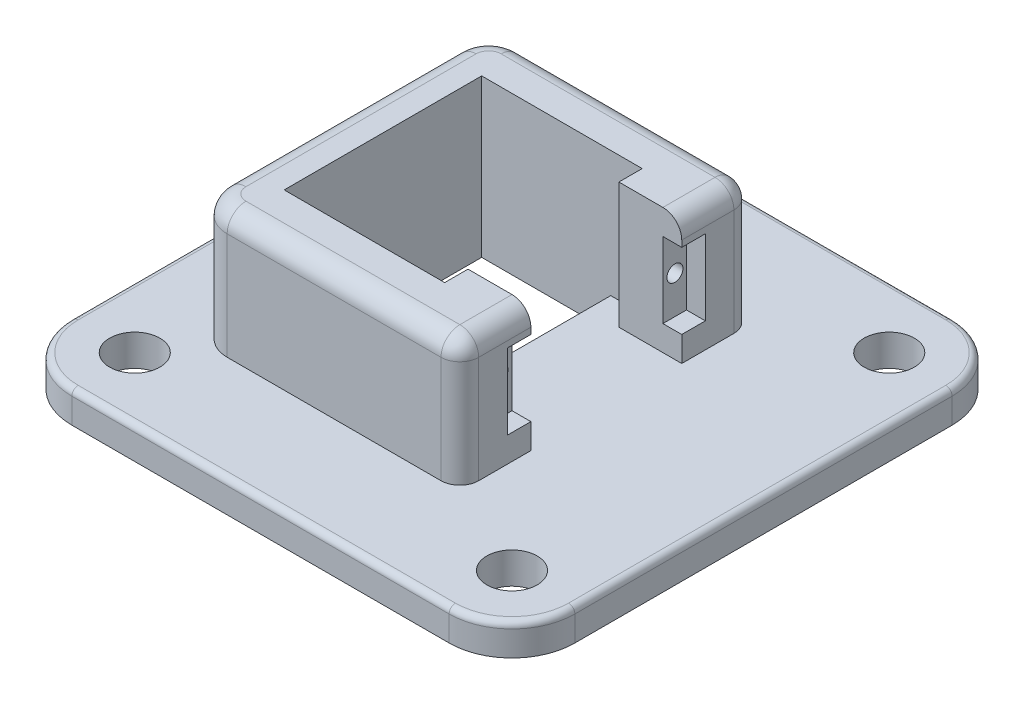
SolidWorks part; units mm, degrees
ref_plane "前视基准面" through (0, 0, 0) normal (0, 0, 1) x (1, 0, 0)
ref_plane "上视基准面" through (0, 0, 0) normal (0, 1, 0) x (1, 0, 0)
ref_plane "右视基准面" through (0, 0, 0) normal (1, 0, 0) x (0, 0, -1)
sketch "草图1" plane through (0, 0, 0) normal (0, 1, 0) x (1, 0, 0)
  line L0 (-40, 40) -> (40, -40) construction
  line L1 (30, 40) -> (-30, 40)
  line L2 (40, 30) -> (40, -30)
  line L3 (30, -40) -> (-30, -40)
  line L4 (-40, 30) -> (-40, -30)
  line L5 (0, -40) -> (0, 40) construction
  line L6 (40, 0) -> (-40, 0) construction
  line L7 (40, 40) -> (-40, -40) construction
  circle A0 centre (-30, 30) radius 4
  circle A1 centre (-30, -30) radius 4
  circle A2 centre (30, -30) radius 4
  circle A3 centre (30, 30) radius 4
  arc A4 (40, -30) -> (30, -40) centre (30, -30) cw
  arc A5 (30, 40) -> (40, 30) centre (30, 30) cw
  arc A6 (-30, -40) -> (-40, -30) centre (-30, -30) cw
  arc A7 (-30, 40) -> (-40, 30) centre (-30, 30) ccw
  point P0 (0, 0)
  point P4 (-30, 30)
  point P5 (30, 30)
  point P6 (-30, -30)
  point P7 (30, -30)
  dimension "D4" = 8
  dimension "D5" = 8
  dimension "D6" = 10
  dimension "D1" = 80
  dimension "D2" = 80
  dimension "D3" = 10
extrude "凸台-拉伸1" add sketch "草图1" along normal blind 5
sketch "草图2" plane through (0, 5, 0) normal (0, 1, 0) x (1, 0, 0)
  line L0 (0, 0) -> (0, -28.3929) construction
  line L2 (-20.5291, -15.7062) -> (0, -15.7062)
  line L3 (-20.5291, -15.7062) -> (-20.5291, 15.7062)
  line L4 (-20.5291, 15.7062) -> (0, 15.7062)
  line L5 (0, -15.7062) -> (0, 15.7062)
  line L6 (-10.2646, 15.7062) -> (-10.2646, -15.7062) construction
  line L7 (-20.5291, 0) -> (0, 0) construction
  point P1 (-10.2646, 0)
extrude "切除-拉伸1" cut sketch "草图2" against normal blind 5
sketch "草图3" plane through (0, 5, 0) normal (0, 1, 0) x (1, 0, 0)
  line L0 (-20.5291, -15.7062) -> (0, -15.7062) construction
  line L1 (0, -15.7062) -> (0, 15.7062) construction
  line L2 (-20.5291, 15.7062) -> (-20.5291, -15.7062) construction
  line L3 (0, 15.7062) -> (-20.5291, 15.7062) construction
  line L4 (40, -30) -> (40, 30)
  line L5 (30, 40) -> (-30, 40)
  line L6 (-40, 30) -> (-40, -30)
  line L7 (-30, -40) -> (30, -40)
  line L8 (40, -30) -> (40, 30)
  line L9 (30, 40) -> (-30, 40)
  line L10 (-40, 30) -> (-40, -30)
  line L11 (-30, -40) -> (30, -40)
  line L12 (-20.5291, -15.7062) -> (0, -15.7062)
  line L13 (0, -15.7062) -> (0, 15.7062)
  line L14 (-20.5291, 15.7062) -> (-20.5291, -15.7062)
  line L15 (0, 15.7062) -> (-20.5291, 15.7062)
  line L16 (0, 15.7062) -> (0, 23.2917)
  line L17 (0, 23.2917) -> (-22.0128, 23.2917)
  line L18 (-27.0128, 18.2917) -> (-27.0128, -18.2917)
  line L19 (-22.0128, -23.2917) -> (0, -23.2917)
  line L20 (0, -23.2917) -> (0, -15.7062)
  line L21 (0, 0) -> (-52.8856, 0) construction
  arc A0 (-27.0128, -18.2917) -> (-22.0128, -23.2917) centre (-22.0128, -18.2917) ccw
  arc A1 (-22.0128, 23.2917) -> (-27.0128, 18.2917) centre (-22.0128, 18.2917) ccw
  arc A4 (30, -40) -> (40, -30) centre (30, -30) ccw
  arc A5 (40, 30) -> (30, 40) centre (30, 30) ccw
  arc A6 (-30, 40) -> (-40, 30) centre (-30, 30) ccw
  arc A7 (-40, -30) -> (-30, -40) centre (-30, -30) ccw
  arc A8 (30, -40) -> (40, -30) centre (30, -30) ccw
  arc A9 (40, 30) -> (30, 40) centre (30, 30) ccw
  arc A10 (-30, 40) -> (-40, 30) centre (-30, 30) ccw
  arc A11 (-40, -30) -> (-30, -40) centre (-30, -30) ccw
  line M13 (-20.5291, 15.7062) -> (0, 15.7062)
  line M15 (0, -15.7062) -> (-20.5291, -15.7062)
  line M16 (-20.5291, -15.7062) -> (-20.5291, 15.7062)
  dimension "D2" = 5
  dimension "D1" = 0
extrude "凸台-拉伸2" add sketch "草图3" along normal blind 20 contours L21 L14 L16 L17 A1 L18 M13 | L21 L18 A0 L19 L20 M16 M15
sketch "草图4" plane through (0, 0, 0) normal (1, 0, 0) x (0, 0, -1)
  line L0 (15.7062, 5) -> (23.2917, 5) construction
  line L1 (23.2917, 5) -> (23.2917, 25) construction
  line L2 (23.2917, 25) -> (15.7062, 25) construction
  line L3 (15.7062, 25) -> (15.7062, 5) construction
  line L4 (-23.2917, 5) -> (-15.7062, 5) construction
  line L5 (-15.7062, 5) -> (-15.7062, 25) construction
  line L6 (-15.7062, 25) -> (-23.2917, 25) construction
  line L7 (-23.2917, 25) -> (-23.2917, 5) construction
  line L8 (15.7062, 5) -> (23.2917, 5)
  line L9 (23.2917, 5) -> (23.2917, 25)
  line L10 (23.2917, 25) -> (15.7062, 25)
  line L11 (15.7062, 25) -> (15.7062, 5)
  line L12 (-23.2917, 5) -> (-15.7062, 5)
  line L13 (-15.7062, 5) -> (-15.7062, 25)
  line L14 (-15.7062, 25) -> (-23.2917, 25)
  line L15 (-23.2917, 25) -> (-23.2917, 5)
extrude "凸台-拉伸3" add sketch "草图4" along normal blind 10
sketch "草图5" plane through (10, 0, 0) normal (1, 0, 0) x (0, 0, -1)
  line L0 (15.7062, 25) -> (15.7062, 5) construction
  line L1 (15.7062, 5) -> (23.2917, 5) construction
  line L2 (23.2917, 5) -> (23.2917, 25) construction
  line L3 (23.2917, 25) -> (15.7062, 25) construction
  line L4 (-23.2917, 25) -> (-23.2917, 5) construction
  line L5 (-23.2917, 5) -> (-15.7062, 5) construction
  line L6 (-15.7062, 5) -> (-15.7062, 25) construction
  line L7 (-15.7062, 25) -> (-23.2917, 25) construction
  line L8 (15.7062, 25) -> (15.7062, 5)
  line L9 (15.7062, 5) -> (23.2917, 5)
  line L10 (23.2917, 5) -> (23.2917, 25)
  line L11 (23.2917, 25) -> (15.7062, 25)
  line L12 (-23.2917, 25) -> (-23.2917, 5)
  line L13 (-23.2917, 5) -> (-15.7062, 5)
  line L14 (-15.7062, 5) -> (-15.7062, 25)
  line L15 (-15.7062, 25) -> (-23.2917, 25)
  line L16 (0, 0) -> (0, 31.2865) construction
  line L17 (-15.7062, 15) -> (15.7062, 15) construction
  line L18 (-15.7062, 25) -> (15.7062, 25) construction
  line L19 (12, 5) -> (-12, 5)
  line L20 (12, 5) -> (12, 25)
  line L21 (12, 25) -> (-12, 25)
  line L22 (-12, 5) -> (-12, 25)
  line L23 (0, 25) -> (0, 5) construction
  line L24 (12, 15) -> (-12, 15) construction
  line L25 (-15.7062, 25) -> (15.7062, 25)
  line L26 (-15.7062, 5) -> (15.7062, 5)
  point P6 (0, 15)
  point P19 (-17.596, 15)
  point P20 (18.3123, 15)
  line M6 (-23.2917, 25) -> (-23.2917, 5)
  line M7 (-23.2917, 5) -> (-15.7062, 5)
  line M8 (-15.7062, 5) -> (-15.7062, 25)
  line M9 (-15.7062, 25) -> (-23.2917, 25)
  dimension "D1" = 24
extrude "凸台-拉伸4" add sketch "草图5" along normal mid plane 10 contours M9 M6 M7 M8 | L26 L22 L25 M8 | L20 L26 L8 L25 | L10 L11 L8 L9
sketch "草图6" plane through (15, 0, 0) normal (1, 0, 0) x (0, 0, -1)
  line L0 (12, 25) -> (12, 5) construction
  line L1 (12, 5) -> (23.2917, 5) construction
  line L2 (23.2917, 5) -> (23.2917, 25) construction
  line L3 (23.2917, 25) -> (12, 25) construction
  line L4 (-12, 25) -> (-23.2917, 25) construction
  line L5 (-23.2917, 25) -> (-23.2917, 5) construction
  line L6 (-23.2917, 5) -> (-12, 5) construction
  line L7 (-12, 5) -> (-12, 25) construction
  line L8 (12, 25) -> (12, 5)
  line L9 (12, 5) -> (23.2917, 5)
  line L10 (23.2917, 5) -> (23.2917, 25)
  line L11 (23.2917, 25) -> (12, 25)
  line L12 (-12, 25) -> (-23.2917, 25)
  line L13 (-23.2917, 25) -> (-23.2917, 5)
  line L14 (-23.2917, 5) -> (-12, 5)
  line L15 (-12, 5) -> (-12, 25)
  line L16 (0, -0.2471) -> (0, 31.1526) construction
  line L17 (-12, 15) -> (12, 15) construction
  line L19 (15.75, 9) -> (-15.75, 9)
  line L20 (15.75, 9) -> (15.75, 21)
  line L21 (15.75, 21) -> (-15.75, 21)
  line L22 (-15.75, 9) -> (-15.75, 21)
  line L23 (0, 21) -> (0, 9) construction
  line L24 (15.75, 15) -> (-15.75, 15) construction
  point P7 (0, 15)
  point P17 (0, 0)
  point P18 (-12, 15)
  point P19 (0, 15)
  dimension "D1" = 31.5
  dimension "D2" = 12
extrude "切除-拉伸2" cut sketch "草图6" against normal blind 3 contours L22 L19 L15 L21 | L20 L21 L8 L19
sketch "草图7" plane through (12, 0, 0) normal (1, 0, 0) x (0, 0, -1)
  line L16 (-12.6725, 15) -> (11.3275, 15) construction
  line L17 (0, 11.6547) -> (0, 19.8582) construction
  circle A0 centre (-13.91, 15) radius 1.275
  circle A1 centre (13.91, 15) radius 1.275
  dimension "D1" = 2.55
  dimension "D2" = 27.82
extrude "切除-拉伸3" cut sketch "草图7" against normal up to next
fillet "圆角1" radius 3 9 edges at (-3.5064, 25, 23.2917) (-25.5483, 25, 21.8272) (-27.0128, 25, 0) (-25.5483, 25, -21.8272) (15, 25, -17.6458) (15, 25, 17.6458) (15, 15, 23.2917) (15, 15, -23.2917) (-3.5064, 25, -23.2917)
fillet "圆角2" radius 1 8 edges at (37.0711, 5, -37.0711) (40, 5, 0) (37.0711, 5, 37.0711) (0, 5, 40) (-37.0711, 5, 37.0711) (-40, 5, 0) (-37.0711, 5, -37.0711) (0, 5, -40)
